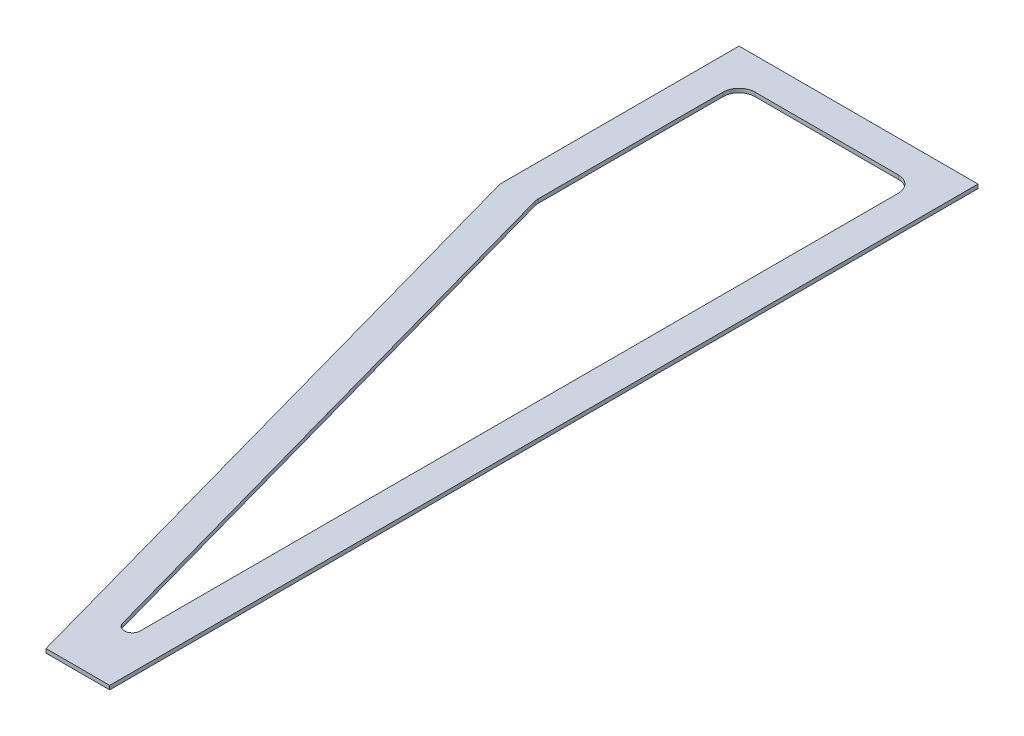
SolidWorks part; units mm, degrees
material "6061 Alloy"
ref_plane "Top Plane" through (0, 0, 0) normal (0, 0, 1) x (1, 0, 0)
ref_plane "Right Plane" through (0, 0, 0) normal (0, 1, 0) x (1, 0, 0)
ref_plane "Front Plane" through (0, 0, 0) normal (1, 0, 0) x (0, 0, -1)
sketch "Sketch1" plane through (0, 0, 0) normal (0, 1, 0) x (1, 0, 0)
  line L0 (0, 0) -> (0, -1384.3)
  line L1 (0, -1384.3) -> (-101.6, -1384.3)
  line L3 (-381, 0) -> (0, 0)
  line L4 (-381, 0) -> (-381, -381)
  line L5 (-381, -381) -> (-101.6, -1384.3)
  line L6 (-329.2689, -377.4021) -> (-75.3779, -1289.1018)
  line L8 (-50.8, -76.2) -> (-50.8, -1286.0199)
  line L9 (-304.8, -50.8) -> (-76.2, -50.8)
  line L10 (-330.2, -76.2) -> (-330.2, -370.588)
  line L11 (-50.8, -50.8) -> (-50.8, -1333.5) construction
  line L12 (-330.2, -50.8) -> (-50.8, -50.8) construction
  line L13 (-330.2, -50.8) -> (-330.2, -374.0586) construction
  line L14 (-330.2, -374.0586) -> (-63.0138, -1333.5) construction
  line L15 (-50.8, -1333.5) -> (-63.0138, -1333.5) construction
  arc A0 (-50.8, -76.2) -> (-76.2, -50.8) centre (-76.2, -76.2) ccw
  arc A1 (-304.8, -50.8) -> (-330.2, -76.2) centre (-304.8, -76.2) ccw
  arc A2 (-329.2689, -377.4021) -> (-330.2, -370.588) centre (-304.8, -370.588) cw
  arc A4 (-75.3779, -1289.1018) -> (-50.8, -1286.0199) centre (-63.4386, -1284.7724) ccw
  dimension "D7" = 25.4
  dimension "D8" = 25.4
  dimension "D1" = 381
  dimension "D2" = 381
  dimension "D3" = 101.6
  dimension "D4" = 1384.3
  dimension "D5" = 0
  dimension "D6" = 50.8
extrude "Boss-Extrude1" add sketch "Sketch1" along normal blind 6.35
